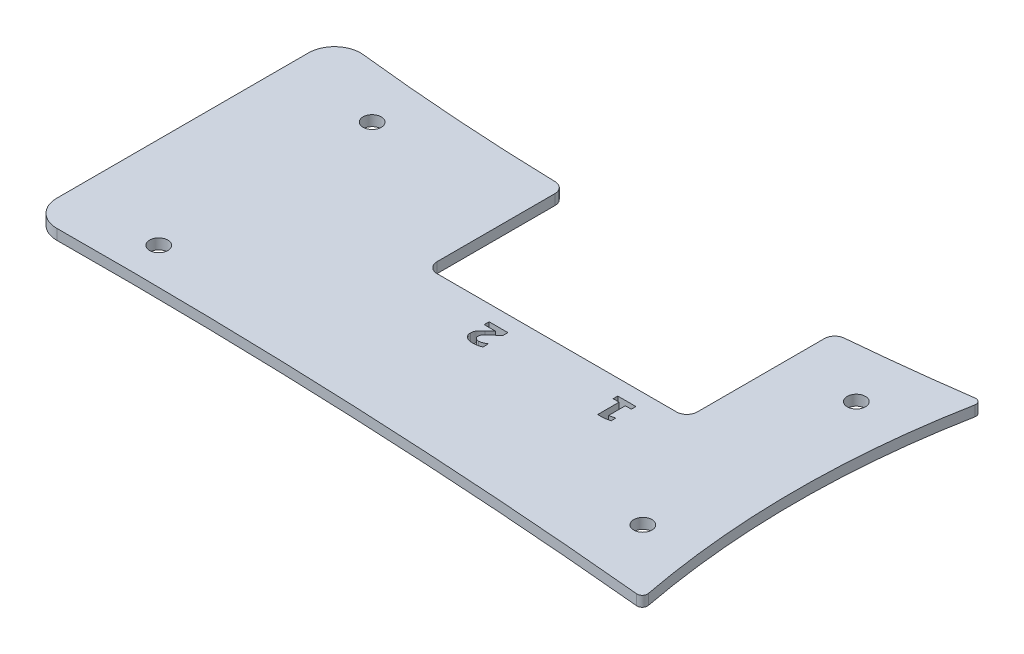
SolidWorks part; units mm, degrees
ref_plane "Alzado" through (0, 0, 0) normal (0, 0, 1) x (1, 0, 0)
ref_plane "Planta" through (0, 0, 0) normal (0, 1, 0) x (1, 0, 0)
ref_plane "Vista lateral" through (0, 0, 0) normal (1, 0, 0) x (0, 0, -1)
sketch "Croquis1" plane through (0, 0, 0) normal (0, 1, 0) x (1, 0, 0)
  line L1 (-5.038, 53.3629) -> (-5.038, 4.9999)
  circle A12 centre (105.5937, 6.9652) radius 2.175
  circle A13 centre (105.5937, 47.9652) radius 2.175
  circle A14 centre (12.5937, 47.9652) radius 2.175
  arc A15 (117.5244, 58.7899) -> (117.5365, -3.9226) centre (281.1497, 27.4652) ccw
  arc A16 (117.5244, 58.7899) -> (116.4035, 59.9683) centre (116.5423, 58.978) ccw
  arc A17 (0.5157, 58.3321) -> (116.4035, 59.9683) centre (51.9534, 519.9785) ccw
  arc A18 (0.5157, 58.3321) -> (-5.038, 53.3629) centre (-0.038, 53.3629) ccw
  arc A19 (-5.038, 4.9999) -> (0, 0) centre (-0.038, 4.9999) ccw
  arc A20 (116.4593, -5.1065) -> (0, 0) centre (8.6221, -1133.9022) ccw
  arc A21 (116.4593, -5.1065) -> (117.5365, -3.9226) centre (116.5544, -4.1111) ccw
  circle A22 centre (12.5937, 6.9652) radius 2.175
extrude "Saliente-Extruir1" add sketch "Croquis1" along normal blind 2
sketch "Croquis2" plane through (0, 2, 0) normal (0, 1, 0) x (1, 0, 0)
  circle A0 centre (12.5937, 6.9652) radius 2.175 construction
  circle A1 centre (105.5937, 6.9652) radius 2.175 construction
  circle A2 centre (105.5937, 47.9652) radius 2.175 construction
  circle A3 centre (12.5937, 47.9652) radius 2.175 construction
  circle A4 centre (12.5937, 6.9652) radius 2.175
  circle A5 centre (105.5937, 6.9652) radius 2.175
  circle A6 centre (105.5937, 47.9652) radius 2.175
  circle A7 centre (12.5937, 47.9652) radius 2.175
  circle A8 centre (12.5937, 47.9652) radius 1.75
  circle A9 centre (105.5937, 47.9652) radius 1.75
  circle A10 centre (105.5937, 6.9652) radius 1.75
  circle A11 centre (12.5937, 6.9652) radius 1.75
  dimension "D1" = 3.5
extrude "Saliente-Extruir2" add sketch "Croquis2" against normal up to surface (2 mm away) up to face at (56.7437, 0, -28.0629)
sketch "Croquis3" plane through (0, 0, 0) normal (0, -1, 0) x (1, 0, 0)
  line L1 (116.5423, -58.978) -> (8.2155, -58.978) construction
  line L7 (92.0423, -58.978) -> (42.0423, -58.978)
  line L8 (92.0423, -58.978) -> (92.0423, -28.978)
  line L9 (92.0423, -28.978) -> (42.0423, -28.978)
  line L10 (42.0423, -58.978) -> (42.0423, -28.978)
  dimension "D4" = 50
  dimension "D5" = 30
  dimension "D6" = 24.5
extrude "Cortar-Extruir1" cut sketch "Croquis3" against normal up to surface (2 mm away) up to face at (56.7437, 2, -28.0629)
fillet "Redondeo1" radius 2 4 edges at (42.0423, 1, -55.5811) (42.0423, 1, -28.978) (92.0423, 1, -57.2085) (92.0423, 1, -28.978)
sketch "Croquis5" plane through (0, 0, 0) normal (0, -1, 0) x (1, 0, 0)
  line L0 (90.0423, -28.978) -> (44.0423, -28.978) construction
  text T0 "1" font "DejaVu Sans" height 5
  text T1 "2" font "DejaVu Sans" height 5
  dimension "D1" = 3
  dimension "D2" = 3
extrude "Cortar-Extruir2" cut sketch "Croquis5" against normal up to surface (2 mm away) up to face at (61.8822, 2, -35.5879)
